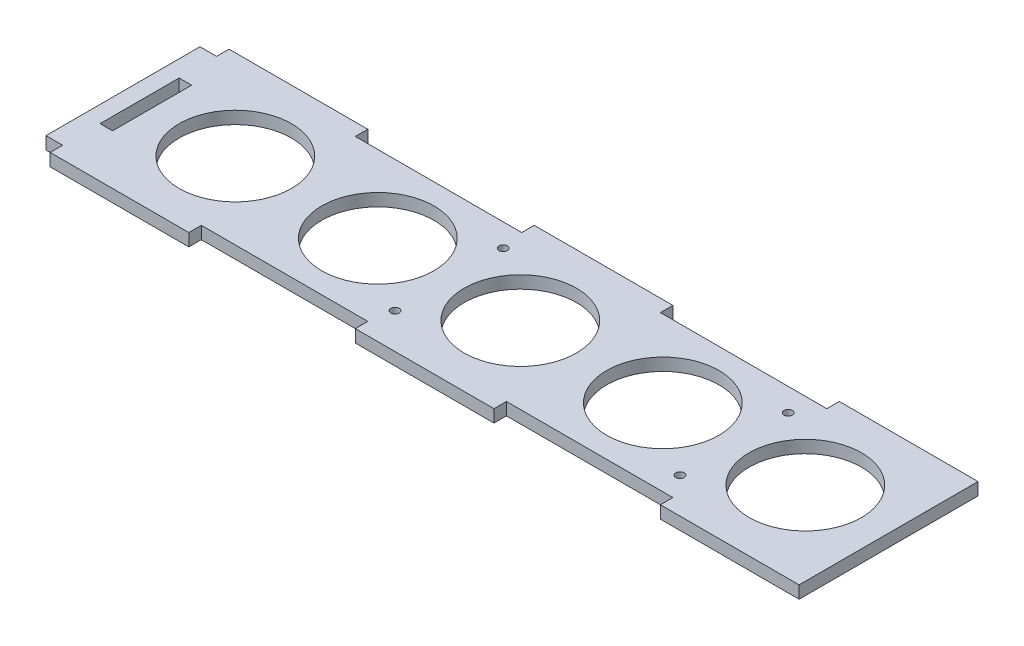
SolidWorks part; units mm, degrees
ref_plane "Front Plane" through (0, 0, 0) normal (0, 0, 1) x (1, 0, 0)
ref_plane "Top Plane" through (0, 0, 0) normal (0, 1, 0) x (1, 0, 0)
ref_plane "Right Plane" through (0, 0, 0) normal (1, 0, 0) x (0, 0, -1)
sketch "Sketch1" plane through (0, 0, 0) normal (0, 1, 0) x (1, 0, 0)
  line L0 (73.3333, 18.5) -> (106.6667, 18.5) construction
  line L1 (0, 21.5) -> (180, 21.5)
  line L2 (0, 21.5) -> (0, -21.5)
  line L3 (0, -21.5) -> (180, -21.5)
  line L4 (180, 21.5) -> (180, -21.5)
  line L5 (0, -9.5) -> (3, -9.5)
  line L6 (0, -9.5) -> (0, 9.5)
  line L7 (0, 9.5) -> (3, 9.5)
  line L8 (3, -9.5) -> (3, 9.5)
  line L9 (33.3333, 21.5) -> (73.3333, 21.5)
  line L10 (33.3333, 21.5) -> (33.3333, 18.5)
  line L11 (33.3333, 18.5) -> (73.3333, 18.5)
  line L12 (73.3333, 21.5) -> (73.3333, 18.5)
  line L13 (106.6667, 21.5) -> (146.6667, 21.5)
  line L14 (106.6667, 21.5) -> (106.6667, 18.5)
  line L15 (106.6667, 18.5) -> (146.6667, 18.5)
  line L16 (146.6667, 21.5) -> (146.6667, 18.5)
  line L17 (146.6667, 18.5) -> (180, 18.5) construction
  line L18 (33.3333, 18.5) -> (0, 18.5) construction
  line L19 (74.375, 0) -> (74.375, 13) construction
  line L20 (106.6667, -18.5) -> (146.6667, -18.5)
  line L21 (146.6667, -21.5) -> (146.6667, -18.5)
  line L22 (106.6667, -21.5) -> (146.6667, -21.5)
  line L23 (106.6667, -21.5) -> (106.6667, -18.5)
  line L24 (33.3333, -18.5) -> (73.3333, -18.5)
  line L25 (73.3333, -21.5) -> (73.3333, -18.5)
  line L26 (33.3333, -21.5) -> (73.3333, -21.5)
  line L27 (33.3333, -21.5) -> (33.3333, -18.5)
  line L28 (23, 0) -> (57.25, 0) construction
  line L29 (57.25, 0) -> (91.5, 0) construction
  line L30 (91.5, 0) -> (125.75, 0) construction
  line L31 (125.75, 0) -> (160, 0) construction
  line L32 (0, 18.5) -> (-4, 18.5)
  line L33 (0, 18.5) -> (0, -18.5)
  line L34 (0, -18.5) -> (-4, -18.5)
  line L35 (-4, 18.5) -> (-4, -18.5)
  line L36 (142.875, 0) -> (142.875, 13) construction
  circle A0 centre (23, 0) radius 13.5
  circle A1 centre (57.25, 0) radius 13.5
  circle A2 centre (91.5, 0) radius 13.5
  circle A3 centre (125.75, 0) radius 13.5
  circle A4 centre (160, 0) radius 13.5
  circle A5 centre (74.375, 13) radius 1
  circle A6 centre (142.875, 13) radius 1
  circle A7 centre (142.875, -13) radius 1
  circle A8 centre (74.375, -13) radius 1
  point P4 (0, 0)
  point P11 (3, 0)
  dimension "D6" = 23
  dimension "D7" = 27
  dimension "D10" = 13
  dimension "D11" = 2
  dimension "D12" = 2
  dimension "D1" = 43
  dimension "D2" = 180
  dimension "D3" = 19
  dimension "D4" = 3
  dimension "D5" = 40
  dimension "D8" = 20
  dimension "D9" = 4
  dimension "D13" = 13
extrude "Boss-Extrude1" add sketch "Sketch1" along normal blind 3 contours L3 L27 L24 L25 L23 L20 L21 L4 L1 L16 L15 L14 L12 L11 L10 L2 L7 L8 L5 A4 A3 A2 A1 A0 | L33 L32 L35 L34
